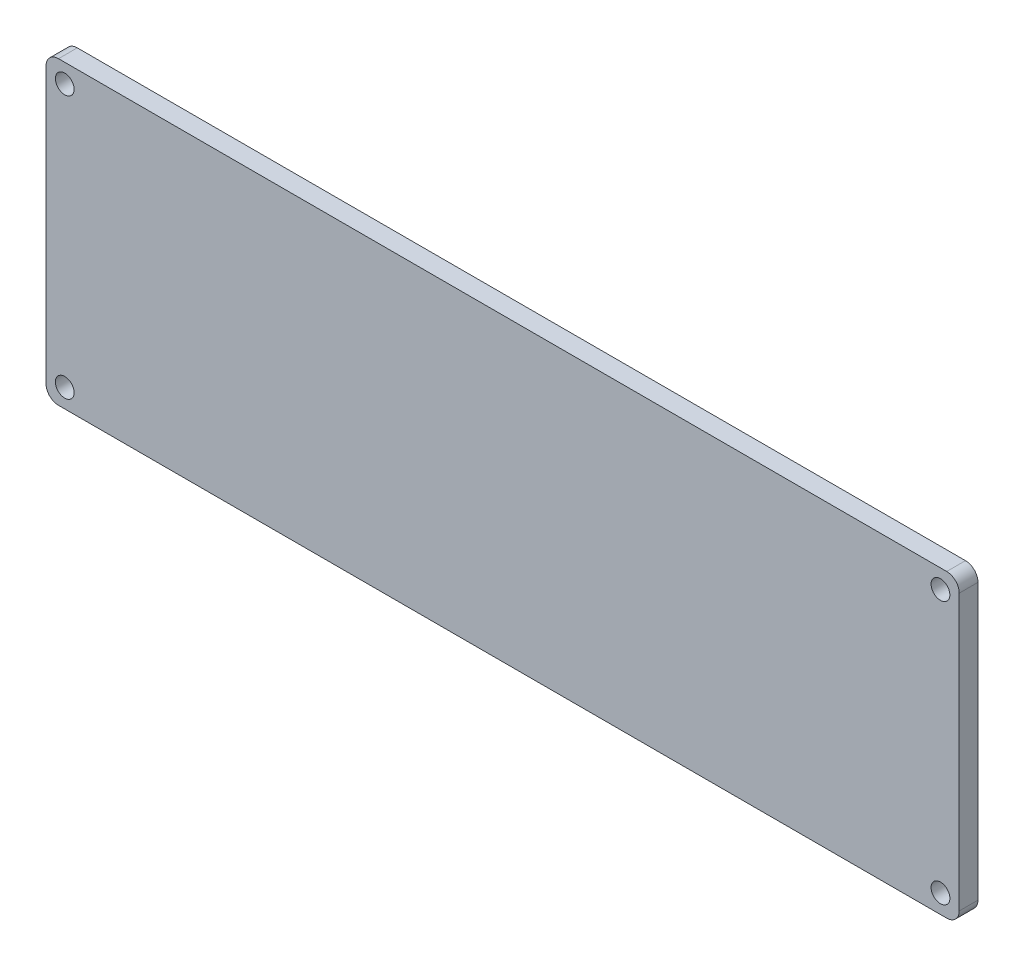
SolidWorks part; units mm, degrees
material "Perspex (TM) GS Acrylic Cast Sheet"
ref_plane "Front Plane" through (0, 0, 0) normal (0, 0, 1) x (1, 0, 0)
ref_plane "Top Plane" through (0, 0, 0) normal (0, 1, 0) x (1, 0, 0)
ref_plane "Right Plane" through (0, 0, 0) normal (1, 0, 0) x (0, 0, -1)
sketch "Sketch1" plane through (0, 0, 0) normal (0, 0, 1) x (1, 0, 0)
  line L0 (3, 45) -> (143, 45)
  line L1 (0, 0) -> (146, 0)
  line L2 (0, 0) -> (0, 48)
  line L3 (0, 48) -> (146, 48)
  line L4 (146, 0) -> (146, 48)
  line L5 (143, 3) -> (143, 45)
  line L6 (3, 3) -> (143, 3)
  line L7 (3, 3) -> (3, 45)
  circle A0 centre (3, 45) radius 1.5
  circle A1 centre (3, 3) radius 1.5
  circle A2 centre (143, 45) radius 1.5
  circle A3 centre (143, 3) radius 1.5
  dimension "D4" = 3
  dimension "D1" = 146
  dimension "D2" = 48
  dimension "D3" = 3
extrude "Boss-Extrude1" add sketch "Sketch1" along normal blind 3 contours L1 L4 L3 L2 A3 L6 A1 L7 A0 L0 A2 L5 | A3 L5 A2 L0 A0 L7 A1 L6
fillet "Fillet1" radius 2 4 edges at (0, 0, 1.5) (146, 0, 1.5) (146, 48, 1.5) (0, 48, 1.5)
